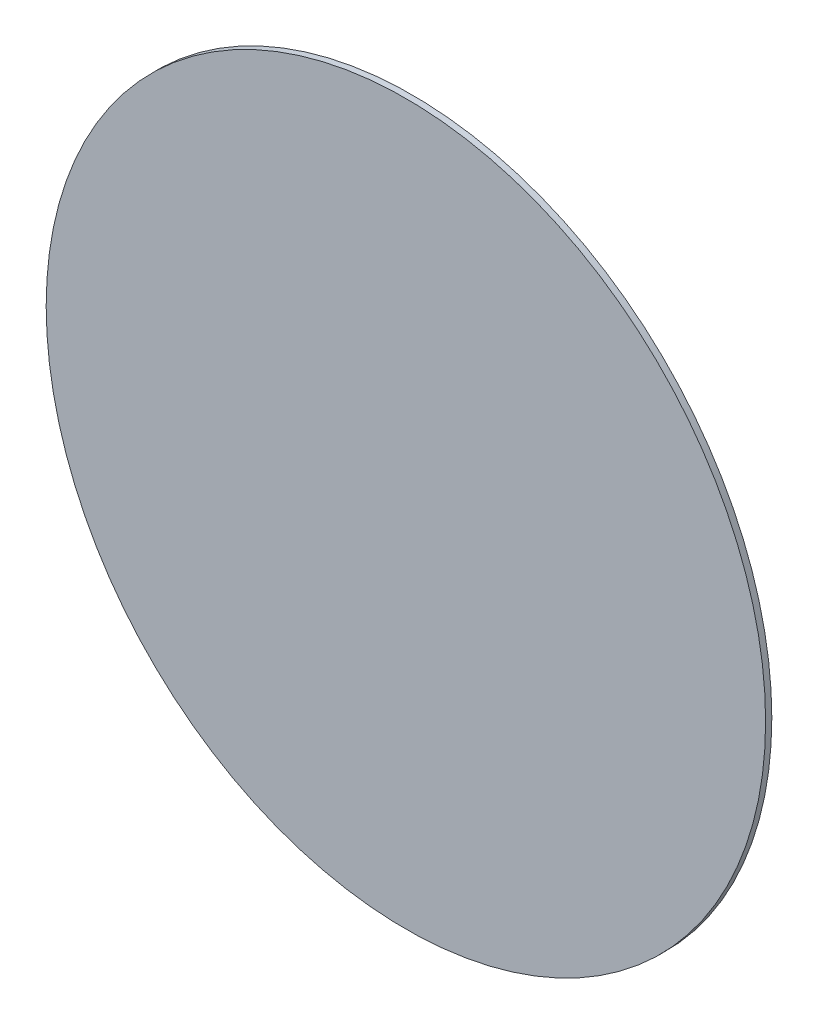
SolidWorks part; units mm, degrees
ref_plane "Front Plane" through (0, 0, 0) normal (0, 0, 1) x (1, 0, 0)
ref_plane "Top Plane" through (0, 0, 0) normal (0, 1, 0) x (1, 0, 0)
ref_plane "Right Plane" through (0, 0, 0) normal (1, 0, 0) x (0, 0, -1)
sketch "Sketch2" plane through (0, 0, 0) normal (0, 0, 1) x (1, 0, 0)
  circle A0 centre (0, 0) radius 200
  dimension "D1" = 400
extrude "Boss-Extrude1" add sketch "Sketch2" along normal mid plane 3.45
